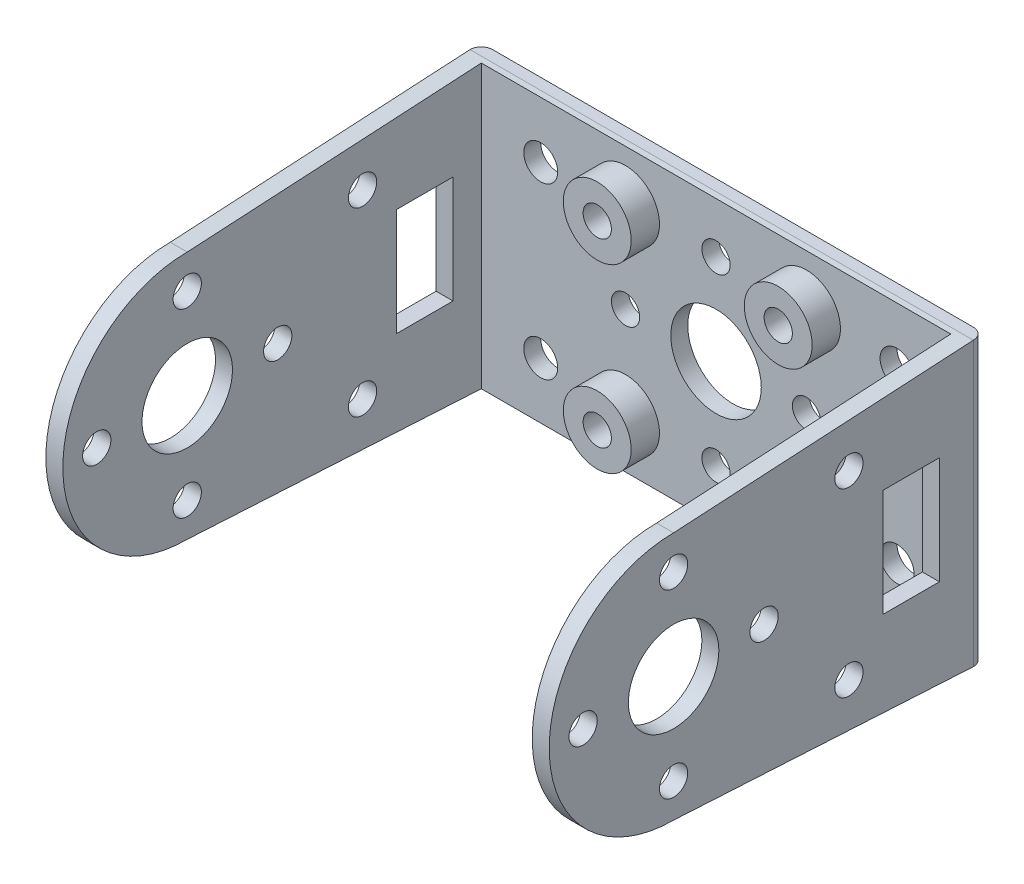
SolidWorks part; units mm, degrees
ref_plane "Front Plane" through (0, 0, 0) normal (0, 0, 1) x (1, 0, 0)
ref_plane "Top Plane" through (0, 0, 0) normal (0, 1, 0) x (1, 0, 0)
ref_plane "Right Plane" through (0, 0, 0) normal (1, 0, 0) x (0, 0, -1)
sketch "Sketch1" plane through (0, 0, 0) normal (0, 0, 1) x (1, 0, 0)
  line L1 (0, 0) -> (44.5, 0)
  line L2 (0, 0) -> (0, 25)
  line L3 (0, 25) -> (44.5, 25)
  line L4 (44.5, 0) -> (44.5, 25)
  dimension "D1" = 44.5
  dimension "D2" = 25
extrude "Boss-Extrude1" add sketch "Sketch1" along normal blind 38.5
sketch "Sketch2" plane through (0, 0, 38.5) normal (0, 0, 1) x (1, 0, 0)
  line L0 (0, 25) -> (0, 0) construction
  line L1 (1.5, 25) -> (43, 25)
  line L2 (1.5, 25) -> (1.5, 0)
  line L3 (1.5, 0) -> (43, 0)
  line L4 (43, 25) -> (43, 0)
  line L5 (0, 0) -> (44.5, 0) construction
  line L6 (44.5, 0) -> (44.5, 25) construction
  point P10 (43, 12.5)
  point P12 (0, 12.5)
  point P13 (1.5, 12.5)
  dimension "D1" = 1.5
  dimension "D2" = 25
  dimension "D3" = 1.5
extrude "Cut-Extrude1" cut sketch "Sketch2" against normal blind 37
fillet "Fillet1" radius 1 2 edges at (44.5, 12.5, 0) (0, 12.5, 0)
sketch "Sketch3" plane through (0, 0, 1.5) normal (0, 0, 1) x (1, 0, 0)
  line L0 (1.5, 25) -> (1.5, 0) construction
  line L3 (43, 25) -> (1.5, 25) construction
  circle A0 centre (14.25, 4.5) radius 3
  circle A1 centre (30.25, 4.5) radius 3
  circle A2 centre (30.25, 20.5) radius 3
  circle A3 centre (14.25, 20.5) radius 3
  dimension "D1" = 6
  dimension "D2" = 12.75
  dimension "D6" = 16
  dimension "D7" = 16
  dimension "D8" = 4.5
  dimension "D4" = 2
  dimension "D5" = 2
extrude "Boss-Extrude2" add sketch "Sketch3" along normal blind 2.5
sketch "Sketch4" plane through (0, 0, 1.5) normal (0, 0, 1) x (1, 0, 0)
  line L1 (1.5, 25) -> (1.5, 0) construction
  line L2 (43, 25) -> (1.5, 25) construction
  circle A0 centre (6.75, 20) radius 1.5
  circle A1 centre (38.25, 20) radius 1.5
  circle A2 centre (38.25, 5) radius 1.5
  circle A3 centre (6.75, 5) radius 1.5
  dimension "D1" = 3
  dimension "D2" = 5.25
  dimension "D6" = 31.5
  dimension "D3" = 5
  dimension "D7" = 15
  dimension "D4" = 2
  dimension "D5" = 2
extrude "Cut-Extrude2" cut sketch "Sketch4" against normal blind 1.5
sketch "Sketch5" plane through (0, 0, 4) normal (0, 0, 1) x (1, 0, 0)
  line L3 (43, 25) -> (1.5, 25) construction
  line L4 (1.5, 25) -> (1.5, 0) construction
  line L5 (1.5, 0) -> (43, 0) construction
  circle A1 centre (22.25, 20.5) radius 1.25
  circle A10 centre (30.25, 20.5) radius 1.25
  circle A11 centre (14.25, 20.5) radius 1.25
  circle A14 centre (22.25, 12.5) radius 4
  circle A15 centre (22.25, 12.5) radius 1.25 [skipped]
  circle A16 centre (30.25, 12.5) radius 1.25
  circle A17 centre (22.25, 4.5) radius 1.25
  circle A18 centre (30.25, 4.5) radius 1.25
  circle A19 centre (14.25, 12.5) radius 1.25
  circle A20 centre (14.25, 4.5) radius 1.25
  circle A21 centre (14.25, 20.5) radius 3 construction
  dimension "D1" = 2.5
  dimension "D2" = 4.5
  dimension "D7" = 3
  dimension "D8" = 3
  dimension "D9" = 8
  dimension "D4" = 8
  dimension "D3" = 12.75
  dimension "D5" = 12.5
  dimension "D6" = 20.75
extrude "Cut-Extrude5" cut sketch "Sketch5" against normal blind 4
sketch "Sketch6" plane through (44.5, 0, 0) normal (1, 0, 0) x (0, 0, -1)
  line L0 (-38.5, 25) -> (-1, 25) construction
  line L1 (-9, 17.5) -> (-4, 17.5)
  line L2 (-9, 17.5) -> (-9, 8)
  line L3 (-9, 8) -> (-4, 8)
  line L4 (-4, 17.5) -> (-4, 8)
  line L5 (0, 25) -> (0, 0) construction
  dimension "D1" = 9.5
  dimension "D2" = 5
  dimension "D3" = 7.5
  dimension "D4" = 4
extrude "Cut-Extrude6" cut sketch "Sketch6" against normal blind 44.5
sketch "Sketch7" plane through (44.5, 0, 0) normal (1, 0, 0) x (0, 0, -1)
  line L0 (-38.5, 0) -> (-1, 0) construction
  line L1 (-38.5, 0) -> (-38.5, 25) construction
  line L2 (-27.5, 23.5) -> (-1, 25)
  line L3 (-27.5, 1.5) -> (-1, 0)
  line L4 (-1, 0) -> (-1, 25) construction
  circle A0 centre (-27.5, 12.5) radius 4
  circle A1 centre (-27.5, 12.5) radius 11
  point P6 (-38.5, 12.5)
  line M12 (-38.5, 0) -> (-1, 0)
  line M14 (-1, 25) -> (-38.5, 25)
  line M15 (-38.5, 25) -> (-38.5, 0)
  dimension "D2" = 8
  dimension "D4" = 22
  dimension "D1" = 12.5
  dimension "D3" = 11
extrude "Cut-Extrude7" cut sketch "Sketch7" against normal blind 44.5 contours A0 | A1 L2 M14 M15 | A1 L3 M15 M12
sketch "Sketch8" plane through (44.5, 0, 0) normal (1, 0, 0) x (0, 0, -1)
  line L2 (-9, 8) -> (-4, 8) construction
  line L3 (-9, 17.5) -> (-9, 8) construction
  circle A0 centre (-19.5, 12.5) radius 1.25
  circle A1 centre (-27.5, 12.5) radius 4 construction
  circle A2 centre (-35.5, 12.5) radius 1.25
  circle A3 centre (-27.5, 4.5) radius 1.25
  circle A4 centre (-12, 4.5) radius 1.25
  circle A5 centre (-12, 20.5) radius 1.25
  circle A6 centre (-27.5, 20.5) radius 1.25
  point P4 (-19.5, 12.5)
  point P11 (-27.5, 4.5)
  point P24 (-27.5, 20.5)
  point P25 (-35.5, 12.5)
  dimension "D6" = 2.5
  dimension "D13" = 3
  dimension "D8" = 8
  dimension "D5" = 0
  dimension "D11" = 5
  dimension "D14" = 4.5
  dimension "D2" = 3
  dimension "D3" = 8
  dimension "D7" = 8
  dimension "D12" = 15.5
  dimension "D4" = 8
  dimension "D15" = 4.5
  dimension "D16" = 9.5
  dimension "D9" = 2
  dimension "D10" = 2
extrude "Cut-Extrude8" cut sketch "Sketch8" against normal blind 44.5
